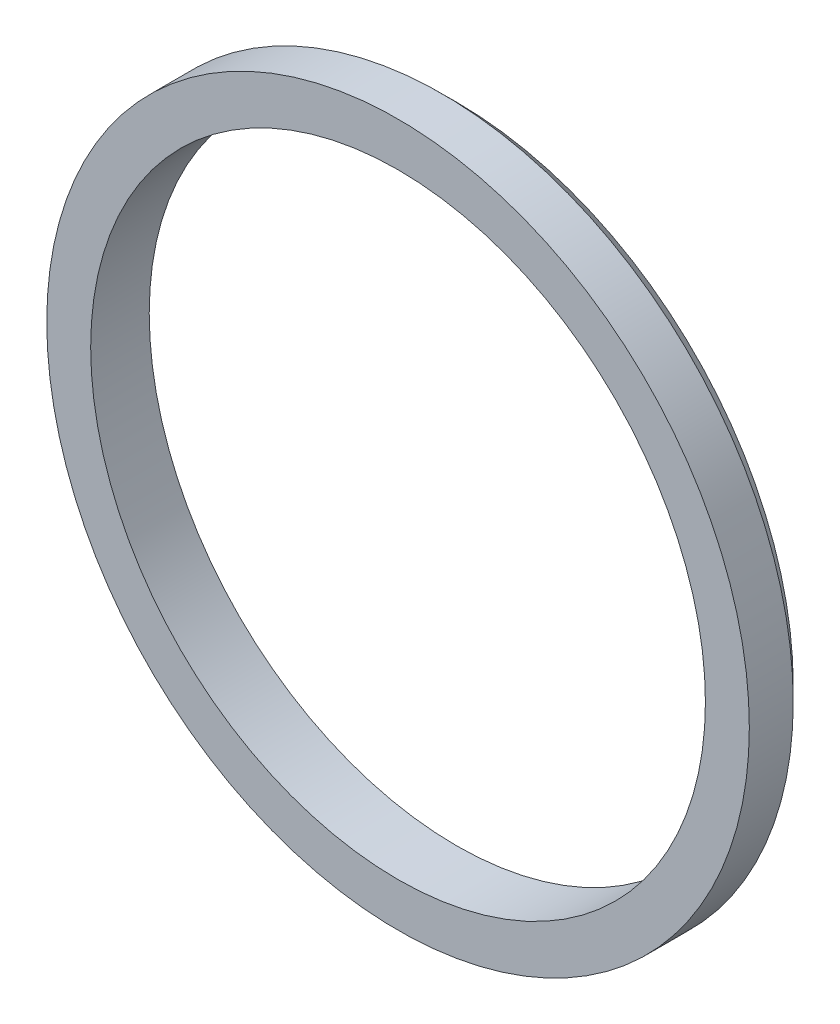
SolidWorks part; units mm, degrees
material "AISI 1035 Acier (SS)"
ref_plane "Plan de face" through (0, 0, 0) normal (0, 0, 1) x (1, 0, 0)
ref_plane "Plan de dessus" through (0, 0, 0) normal (0, 1, 0) x (1, 0, 0)
ref_plane "Plan de droite" through (0, 0, 0) normal (1, 0, 0) x (0, 0, -1)
sketch "Esquisse1" plane through (0, 0, 0) normal (0, 0, 1) x (1, 0, 0)
  circle A0 centre (0, 0) radius 12
  circle A1 centre (0, 0) radius 10.5
  dimension "D1" = 21
  dimension "D2" = 24
extrude "Boss.-Extru.1" add sketch "Esquisse1" along normal mid plane 2
chamfer "Chanfrein1" distance 0.5 angle 45 1 edges at (12, 0, -1)
